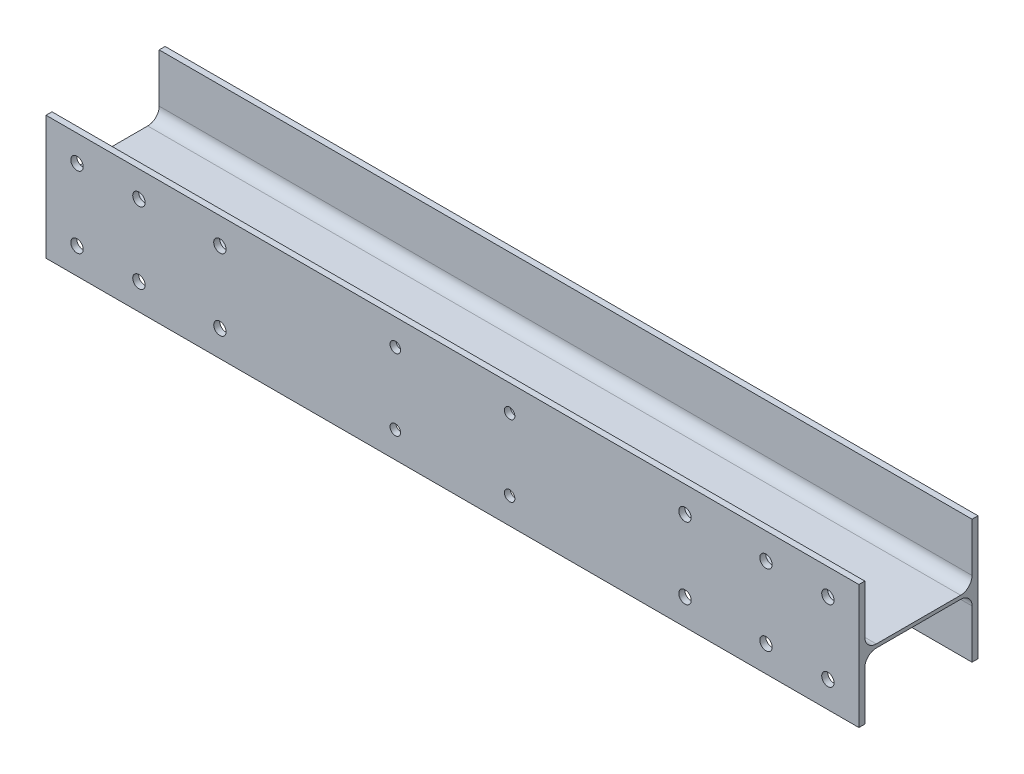
SolidWorks part; units mm, degrees
material "1.0038 (S235JRG2)"
ref_plane "Ebene vorne" through (0, 0, 0) normal (0, 0, 1) x (1, 0, 0)
ref_plane "Ebene oben" through (0, 0, 0) normal (0, 1, 0) x (1, 0, 0)
ref_plane "Ebene rechts" through (0, 0, 0) normal (1, 0, 0) x (0, 0, -1)
sketch "Länge" plane through (0, 0, 0) normal (0, 0, 1) x (1, 0, 0)
  line L0 (853, 0) -> (-853, 0)
  point P3 (0, 0)
  dimension "D1" = 1706
other "Strukturbauteil1"
ref_plane "Ebene1" through (853, 0, 0) normal (-1, 0, 0) x (0, -1, 0)
sketch "Skizze12" plane through (853, 0, 0) normal (-1, 0, 0) x (0, -1, 0)
  line L0 (130, 125) -> (-130, 125)
  line L1 (-130, 125) -> (-130, 112.5)
  line L2 (-130, 112.5) -> (-27.75, 112.5)
  line L3 (-3.75, -88.5) -> (-3.75, 88.5)
  line L4 (-27.75, -112.5) -> (-130, -112.5)
  line L5 (-130, -112.5) -> (-130, -125)
  line L6 (-130, -125) -> (130, -125)
  line L7 (130, -125) -> (130, -112.5)
  line L8 (130, -112.5) -> (27.75, -112.5)
  line L9 (3.75, -88.5) -> (3.75, 88.5)
  line L10 (27.75, 112.5) -> (130, 112.5)
  line L11 (130, 112.5) -> (130, 125)
  line L12 (-49, 125) -> (-49, 112.5) construction
  line L13 (0, -125) -> (0, 125) construction
  line L14 (-3.75, 0) -> (3.75, 0) construction
  line L15 (-77, 125) -> (-77, 112.5) construction
  line L16 (-63, 125) -> (-63, 112.5) construction
  line L17 (49, 125) -> (49, 112.5) construction
  line L18 (63, 125) -> (63, 112.5) construction
  line L19 (77, 125) -> (77, 112.5) construction
  line L20 (-77, -112.5) -> (-77, -125) construction
  line L21 (-63, -112.5) -> (-63, -125) construction
  line L22 (-49, -112.5) -> (-49, -125) construction
  line L23 (49, -112.5) -> (49, -125) construction
  line L24 (63, -112.5) -> (63, -125) construction
  line L25 (77, -112.5) -> (77, -125) construction
  line L26 (-77, -118.75) -> (-63, -118.75) construction
  line L27 (-63, -118.75) -> (-49, -118.75) construction
  line L28 (49, -118.75) -> (63, -118.75) construction
  line L29 (63, -118.75) -> (77, -118.75) construction
  arc A0 (-3.75, 88.5) -> (-27.75, 112.5) centre (-27.75, 88.5) ccw
  arc A1 (-27.75, -112.5) -> (-3.75, -88.5) centre (-27.75, -88.5) ccw
  arc A2 (3.75, -88.5) -> (27.75, -112.5) centre (27.75, -88.5) ccw
  arc A3 (27.75, 112.5) -> (3.75, 88.5) centre (27.75, 88.5) ccw
  point P21 (-130, -125)
  point P22 (0, 0)
  point P25 (0, -125)
  point P28 (130, -125)
  point P29 (130, 125)
  point P30 (0, 125)
  point P31 (-130, 125)
  point P32 (-130, 0)
  point P33 (130, 0)
  point P63 (0, 0)
  dimension "r" = 24
  dimension "h" = 250
  dimension "b" = 260
  dimension "tg" = 12.5
  dimension "ts" = 7.5
  dimension "w" = 126
  dimension "dl" = 28
sketch "Skizze2" plane through (0, 0, 125) normal (0, 0, 1) x (1, 0, 0)
  line L0 (0, 0) -> (-488, 0) construction
  line L1 (-788, 75) -> (-658, 75) construction
  line L2 (-788, 75) -> (-788, -75) construction
  line L3 (-788, -75) -> (-658, -75) construction
  line L4 (-853, -130) -> (-853, 130) construction
  line L5 (-658, 75) -> (-488, 75) construction
  line L6 (-658, 75) -> (-658, -75) construction
  line L7 (-658, -75) -> (-488, -75) construction
  line L8 (-488, 75) -> (-488, -75) construction
  line L9 (0, 130) -> (0, -130) construction
  line L10 (-853, 130) -> (853, 130) construction
  line L11 (-853, -130) -> (853, -130) construction
  circle A0 centre (-788, 75) radius 13
  circle A1 centre (-788, -75) radius 13
  circle A2 centre (-658, -75) radius 13
  circle A3 centre (-658, 75) radius 13
  circle A4 centre (-488, 75) radius 13
  circle A5 centre (-488, -75) radius 13
  circle A6 centre (488, -75) radius 13
  circle A7 centre (488, 75) radius 13
  circle A8 centre (658, 75) radius 13
  circle A9 centre (658, -75) radius 13
  circle A10 centre (788, -75) radius 13
  circle A11 centre (788, 75) radius 13
  circle A12 centre (-120, 75) radius 11
  circle A13 centre (120, 75) radius 11
  circle A14 centre (-120, -75) radius 11
  circle A15 centre (120, -75) radius 11
  dimension "D4" = 26
  dimension "D6" = 22
  dimension "D7" = 240
  dimension "D8" = 150
  dimension "D1" = 170
  dimension "D2" = 130
  dimension "D3" = 150
  dimension "D5" = 65
extrude "Schnitt-Linear austragen1" cut sketch "Skizze2" against normal up to surface (12.5 mm away) up to face at (0, 78.875, 112.5)
